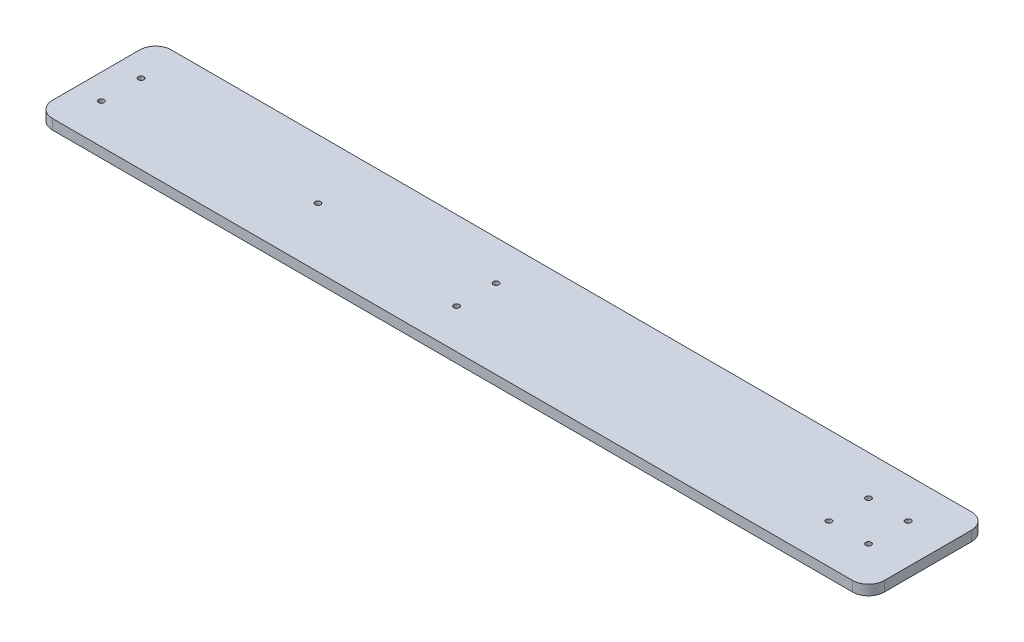
SolidWorks part; units mm, degrees
ref_plane "Front Plane" through (0, 0, 0) normal (0, 0, 1) x (1, 0, 0)
ref_plane "Top Plane" through (0, 0, 0) normal (0, 1, 0) x (1, 0, 0)
ref_plane "Right Plane" through (0, 0, 0) normal (1, 0, 0) x (0, 0, -1)
sketch "Sketch12" plane through (0, 0, 0) normal (0, 1, 0) x (1, 0, 0)
  line L1 (-262.5, 37.5) -> (262.5, 37.5)
  line L2 (-262.5, 37.5) -> (-262.5, -37.5)
  line L3 (-262.5, -37.5) -> (262.5, -37.5)
  line L4 (262.5, 37.5) -> (262.5, -37.5)
  line L5 (-262.5, 37.5) -> (262.5, -37.5) construction
  line L6 (-262.5, -37.5) -> (262.5, 37.5) construction
  point P0 (0, 0)
  dimension "D1" = 525
  dimension "D2" = 75
extrude "Boss-Extrude2" add sketch "Sketch12" along normal blind 6.35
sketch "Sketch13" plane through (0, 0, 0) normal (0, -1, 0) x (1, 0, 0)
  line L0 (262.5, -37.5) -> (-262.5, -37.5) construction
  line L2 (262.5, 37.5) -> (262.5, -37.5) construction
  circle A0 centre (212.5, -12.5) radius 1.75
  point P4 (262.5, 0)
  dimension "D1" = 25
  dimension "D3" = 3.5
  dimension "D2" = 50
extrude "Cut-Extrude1" cut sketch "Sketch13" against normal through all
pattern_linear "LPattern1" count 2 spacing 25 along (1, 0, 0) of "Cut-Extrude1"
pattern_linear "LPattern2" count 2 spacing 25 along (0, 0, 1) of "LPattern1", "Cut-Extrude1"
sketch "Sketch15" plane through (0, 0, 0) normal (0, -1, 0) x (1, 0, 0)
  line L0 (262.5, 37.5) -> (262.5, -37.5) construction
  line L1 (-262.5, 37.5) -> (262.5, 37.5) construction
  circle A0 centre (-122.5, 0) radius 1.75
  dimension "D1" = 385
  dimension "D2" = 3.5
  dimension "D3" = 37.5
extrude "Cut-Extrude2" cut sketch "Sketch15" against normal through all
fillet "Fillet1" radius 10 4 edges at (262.5, 3.175, -37.5) (262.5, 3.175, 37.5) (-262.5, 3.175, 37.5) (-262.5, 3.175, -37.5)
sketch "Sketch17" plane through (0, 6.35, 0) normal (0, 1, 0) x (1, 0, 0)
  line L0 (-252.5, -37.5) -> (252.5, -37.5) construction
  line L1 (252.5, 37.5) -> (-252.5, 37.5) construction
  circle A0 centre (-22.5, 12.5) radius 1.75
  circle A1 centre (-22.5, -12.5) radius 1.75
  dimension "D1" = 3.5
  dimension "D2" = 3.5
  dimension "D3" = 100
  dimension "D4" = 100
  dimension "D5" = 25
  dimension "D6" = 25
extrude "Cut-Extrude3" cut sketch "Sketch17" against normal through all
sketch "Sketch18" plane through (0, 6.35, 0) normal (0, 1, 0) x (1, 0, 0)
  line L0 (-262.5, 27.5) -> (-262.5, -27.5) construction
  line L1 (252.5, 37.5) -> (-252.5, 37.5) construction
  line L2 (-252.5, -37.5) -> (252.5, -37.5) construction
  circle A0 centre (-246.62, 12.5) radius 1.75
  circle A1 centre (-246.62, -12.5) radius 1.75
  dimension "D1" = 3.5
  dimension "D2" = 3.5
  dimension "D3" = 15.88
  dimension "D4" = 15.88
  dimension "D5" = 25
  dimension "D6" = 25
extrude "Cut-Extrude4" cut sketch "Sketch18" against normal through all
